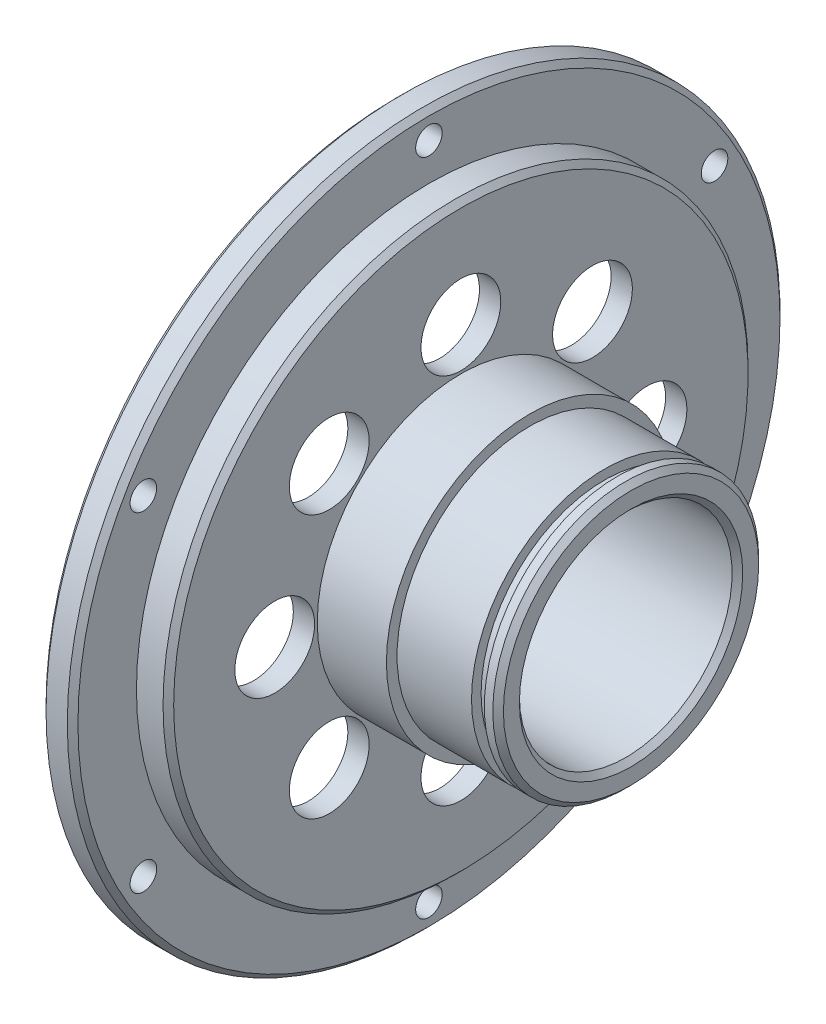
SolidWorks part; units mm, degrees
material "6061 合金"
ref_plane "前视基准面" through (0, 0, 0) normal (0, 0, 1) x (1, 0, 0)
ref_plane "上视基准面" through (0, 0, 0) normal (0, 1, 0) x (1, 0, 0)
ref_plane "右视基准面" through (0, 0, 0) normal (1, 0, 0) x (0, 0, -1)
sketch "草图1" plane through (0, 0, 0) normal (0, 0, 1) x (1, 0, 0)
  line L0 (0, 33.5) -> (0, 25.5)
  line L1 (0, 25.5) -> (4, 25.5)
  line L2 (4, 25.5) -> (4, 9)
  line L3 (4, 9) -> (6, 9)
  line L4 (6, 9) -> (6, 10)
  line L5 (6, 10) -> (22, 10)
  line L6 (22, 10) -> (22, 13.5)
  line L7 (22, 13.5) -> (20.7, 13.5)
  line L8 (20.7, 13.5) -> (20.7, 11.6)
  line L9 (20.7, 11.6) -> (19.5, 11.6)
  line L10 (19.5, 11.6) -> (19.5, 13.5)
  line L11 (19.5, 13.5) -> (6, 13.5)
  line L12 (6, 13.5) -> (6, 27.5)
  line L13 (6, 27.5) -> (3, 27.5)
  line L14 (3, 27.5) -> (3, 33.5)
  line L15 (3, 33.5) -> (0, 33.5)
  line L16 (0, 0) -> (35.3159, 0) construction
  dimension "D1" = 67
  dimension "D2" = 55
  dimension "D3" = 27
  dimension "D4" = 22
  dimension "D5" = 20
  dimension "D6" = 18
  dimension "D7" = 51
  dimension "D8" = 3
  dimension "D9" = 6
  dimension "D10" = 2
  dimension "D11" = 2
  dimension "D12" = 1.3
  dimension "D13" = 1.2
  dimension "D14" = 23.2
revolve "旋转1" add sketch "草图1" angle 360 about L16
chamfer "倒角1" distance 0.5 angle 45 7 edges at (3, 0, 33.5) (0, 0, 33.5) (4, 0, 9) (22, 0, 10) (22, 0, 13.5) (6, 0, 27.5) (0, 0, 25.5)
sketch "草图2" plane through (6, 0, 0) normal (1, 0, 0) x (0, 0, -1)
  circle A0 centre (0, 0) radius 17.5 construction
  circle A1 centre (0, -17.5) radius 3.75
  circle A2 centre (0, 17.5) radius 3.75
  circle A3 centre (12.3744, 12.3744) radius 3.75
  circle A4 centre (17.5, 0) radius 3.75
  circle A5 centre (12.3744, -12.3744) radius 3.75
  circle A6 centre (-12.3744, -12.3744) radius 3.75
  circle A7 centre (-17.5, 0) radius 3.75
  circle A8 centre (-12.3744, 12.3744) radius 3.75
  point P14 (0, 0)
  dimension "D1" = 35
  dimension "D2" = 7.5
  dimension "D3" = 8
extrude "切除-拉伸1" cut sketch "草图2" against normal blind 10
sketch "草图3" plane through (3, 0, 0) normal (1, 0, 0) x (0, 0, -1)
  circle A0 centre (0, 0) radius 31 construction
  dimension "D1" = 62
hole_wizard "M3 螺纹孔1" positions "草图4" profile "草图5" tap size "M3" standard "GB"
sketch "草图4" plane through (3, 0, 0) normal (1, 0, 0) x (0, 0, -1)
  line L0 (0, 31) -> (0, 0) construction
  circle A0 centre (0, 0) radius 31 construction
  point P0 (0, 31)
sketch "草图5" plane through (3, 31, 0) normal (0, 1, 0) x (0, 0, -1)
  line L0 (0, 0) -> (0, 8.2511)
  line L1 (0, 8.2511) -> (1.25, 7.5)
  line L2 (1.25, 7.5) -> (1.25, 0)
  line L5 (1.25, 0) -> (0, 0)
  line L10 (0, 8.2511) -> (-1.25, 7.5) construction
  line L11 (0, -6.35) -> (0, 107.95) construction
  dimension "螺纹孔钻头直径" = 2.5
  dimension "螺纹孔钻头深度" = 7.5
  dimension "导头角度" = 118
cosmetic thread "孔螺蚊线1" parameters "D1"=6, "D2"=3
pattern_circular "阵列(圆周)1" count 6 over 360 about axis through (0, 0, 0) along (1, 0, 0) of "M3 螺纹孔1"
cosmetic thread "孔螺蚊线2" parameters "D1"=6, "D2"=3
cosmetic thread "孔螺蚊线3" parameters "D1"=6, "D2"=3
cosmetic thread "孔螺蚊线4" parameters "D1"=6, "D2"=3
cosmetic thread "孔螺蚊线5" parameters "D1"=6, "D2"=3
cosmetic thread "孔螺蚊线6" parameters "D1"=6, "D2"=3
sketch "草图6" plane through (22, 0, 0) normal (1, 0, 0) x (0, 0, -1)
  circle A0 centre (0, 0) radius 12.5
  dimension "D1" = 25
extrude "切除-拉伸2" cut sketch "草图6" against normal blind 9.5 flip side to cut
chamfer "倒角2" distance 0.5 angle 45 1 edges at (22, 0, -12.5)
